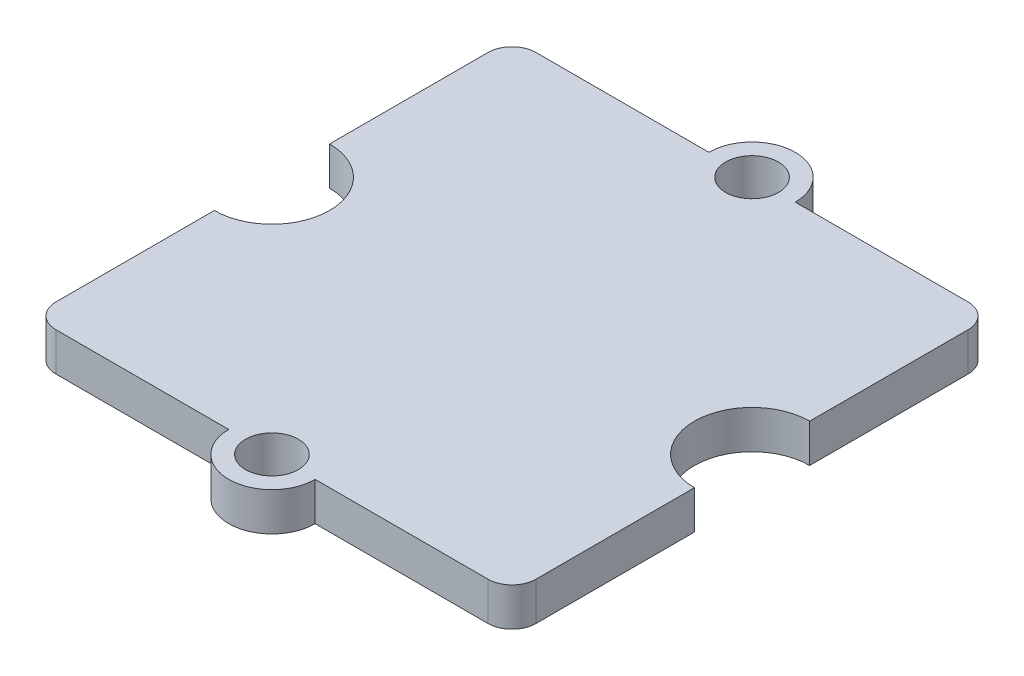
SolidWorks part; units mm, degrees
ref_plane "Plan de face" through (0, 0, 0) normal (0, 0, 1) x (1, 0, 0)
ref_plane "Plan de dessus" through (0, 0, 0) normal (0, 1, 0) x (1, 0, 0)
ref_plane "Plan de droite" through (0, 0, 0) normal (1, 0, 0) x (0, 0, -1)
sketch "Esquisse1" plane through (0, 0, 0) normal (0, 1, 0) x (1, 0, 0)
  line L1 (-9, -10) -> (9, -10)
  line L2 (-10, -9) -> (-10, 9)
  line L3 (-9, 10) -> (9, 10)
  line L4 (10, -9) -> (10, 9)
  line L5 (-10, -10) -> (10, 10) construction
  line L6 (-10, 10) -> (10, -10) construction
  circle A0 centre (0, 10) radius 1.8
  circle A1 centre (0, -10) radius 1.8
  circle A2 centre (-10, 0) radius 2.4
  circle A3 centre (10, 0) radius 2.4
  circle A4 centre (0, 10) radius 1.1
  arc A5 (9, 10) -> (10, 9) centre (9, 9) cw
  circle A6 centre (0, -10) radius 1.1
  arc A7 (-9, -10) -> (-10, -9) centre (-9, -9) cw
  arc A8 (9, -10) -> (10, -9) centre (9, -9) ccw
  arc A9 (-10, 9) -> (-9, 10) centre (-9, 9) cw
  point P0 (0, 0)
  dimension "D2" = 1
  dimension "D3" = 4.8
  dimension "D4" = 2.2
  dimension "D5" = 3.6
  dimension "D1" = 20
extrude "Boss.-Extru.1" add sketch "Esquisse1" along normal blind 1.6 contours A9 L2 A2 A7 L1 A1 A8 L4 A3 A5 L3 A0 | A4 L3 A0 | A4 L3 A0 | A6 L1 A1 | A6 L1 A1
